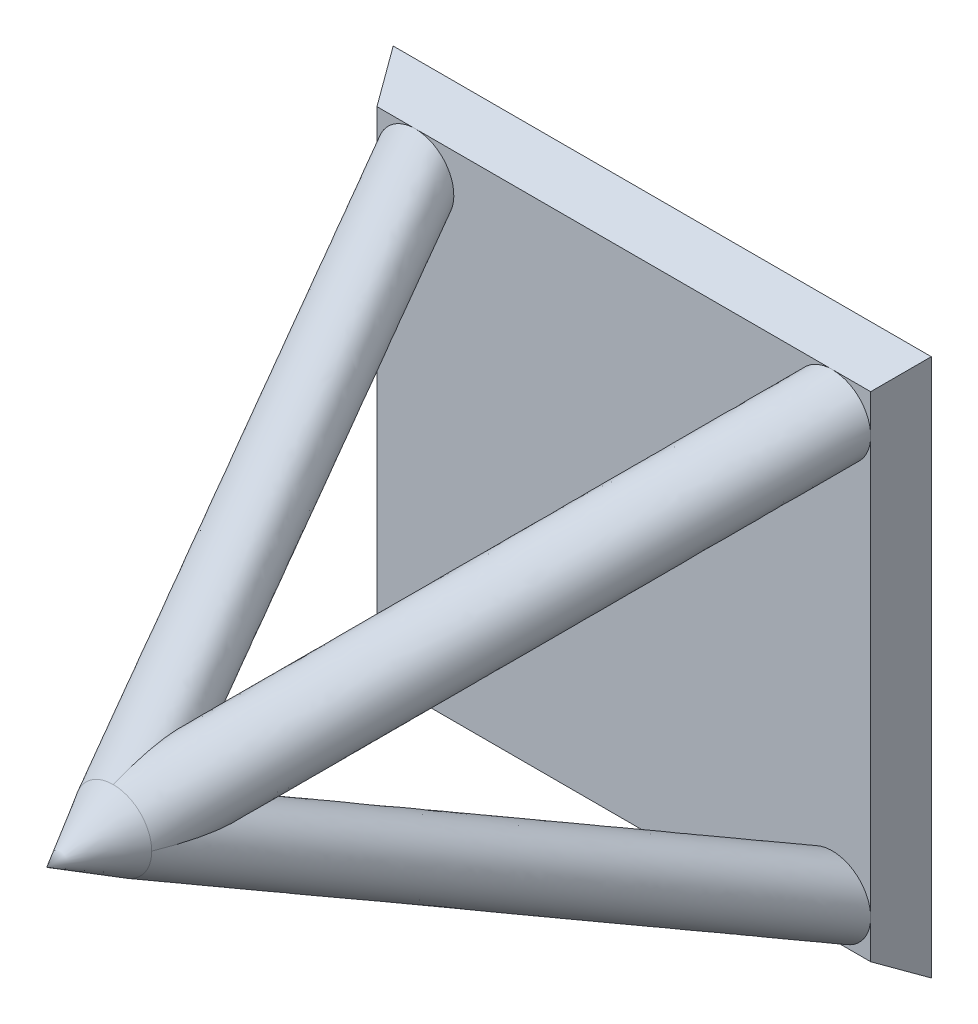
SolidWorks part; units mm, degrees
ref_plane "Front" through (0, 0, 0) normal (0, 0, 1) x (1, 0, 0)
ref_plane "Top" through (0, 0, 0) normal (0, 1, 0) x (1, 0, 0)
ref_plane "Right" through (0, 0, 0) normal (1, 0, 0) x (0, 0, -1)
sketch "Sketch1" plane through (0, 0, 0) normal (0, 0, 1) x (1, 0, 0)
  line L0 (0, 0) -> (0, 43.0475) construction
  line L1 (-7, 7) -> (7, 7)
  line L2 (-7, 7) -> (-7, -7)
  line L3 (-7, -7) -> (7, -7)
  line L4 (7, 7) -> (7, -7)
  line L5 (0, 0) -> (74.4916, 0) construction
  point P7 (0, 7)
  point P8 (7, 0)
  dimension "D1" = 14
  dimension "D2" = 14
extrude "Boss-Extrude1" add sketch "Sketch1" along normal blind 1 draft 30
sketch "Sketch2" plane through (0, 0, 1) normal (0, 0, 1) x (1, 0, 0)
  line L0 (6.4226, -6.4226) -> (6.4226, 6.4226) construction
  line L1 (6.4226, 6.4226) -> (-6.4226, 6.4226) construction
  circle A0 centre (5.4226, 5.4226) radius 1
  dimension "D1" = 2
ref_plane "Plane1" through (0, 0, 0) normal (0.7071, -0.7071, 0) x (0, 0, -1)
sketch "Sketch3" plane through (0, 0, 0) normal (0.7071, -0.7071, 0) x (0, 0, -1)
  line L0 (-1, 7.6688) -> (-14.2827, 0)
  line L1 (0, 0) -> (-12.2099, 0) construction
sweep "Sweep1" add profiles "Sketch2" path "Sketch3"
ref_axis "Axis1" through (0, 0, -4.2318) along (0, 0, 1)
pattern_circular "CirPattern1" count 4 over 360 about axis through (0, 0, -4.2318) along (0, 0, 1) of "Sweep1"
sketch "Sketch4" plane through (0, 0, 14.2827) normal (0, 0, 1) x (1, 0, 0)
  circle A0 centre (0, 0) radius 1
extrude "Boss-Extrude2" add sketch "Sketch4" along normal blind 10 draft 30
